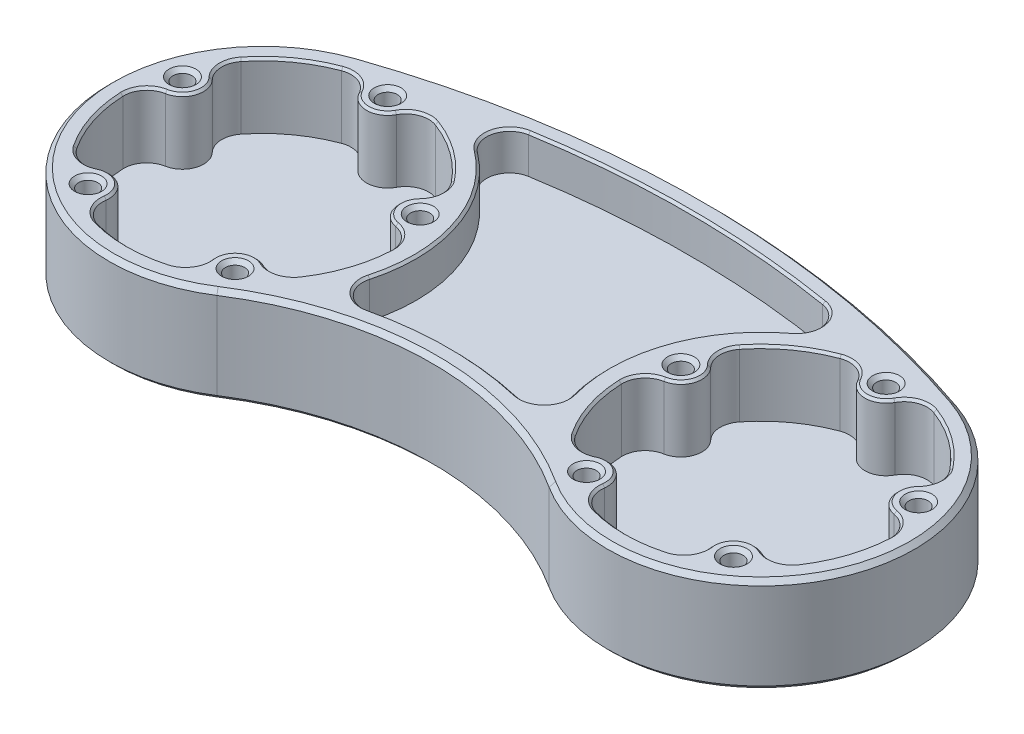
SolidWorks part; units mm, degrees
ref_plane "Front Plane" through (0, 0, 0) normal (0, 0, 1) x (1, 0, 0)
ref_plane "Top Plane" through (0, 0, 0) normal (0, 1, 0) x (1, 0, 0)
ref_plane "Right Plane" through (0, 0, 0) normal (1, 0, 0) x (0, 0, -1)
sketch "Sketch1" plane through (0, 0, 0) normal (0, 1, 0) x (1, 0, 0)
  line L0 (0, 0) -> (0, 64.0532) construction
  line L1 (0, 0) -> (101.1734, 0) construction
  line L2 (-41.275, 25.4) -> (41.275, 25.4) construction
  circle A0 centre (-41.275, 0) radius 25.4
  circle A1 centre (41.275, 0) radius 25.4
  arc A3 (-27.5167, -21.3511) -> (27.5167, -21.3511) centre (0, -64.0532) cw
  arc A4 (-49.53, 24.0211) -> (49.53, 24.0211) centre (0, -120.1057) cw
  dimension "D1" = 82.55
  dimension "D2" = 50.8
  dimension "D3" = 50.8
  dimension "D4" = 152.4
extrude "Boss-Extrude1" add sketch "Sketch1" along normal mid plane 15.875
sketch "Sketch2" plane through (0, 7.9375, 0) normal (0, 1, 0) x (1, 0, 0)
  line L0 (0, 0) -> (0, 31.4381) construction
  circle A0 centre (-41.275, 0) radius 22.225
  arc A1 (-49.53, 24.0211) -> (-27.5167, -21.3511) centre (-41.275, 0) ccw construction
  circle A2 centre (41.275, 0) radius 22.225
  dimension "D1" = 3.175
extrude "Cut-Extrude1" cut sketch "Sketch2" along a picked direction on the side against the normal offset from surface (10.795 mm away) 5.08
sketch "Sketch3" plane through (0, 7.9375, 0) normal (0, 1, 0) x (1, 0, 0)
  arc A0 (24.3588, 27.1178) -> (26.0244, 20.3121) centre (23.7369, 23.3589) cw
  arc A1 (16.7919, -6.7628) -> (12.2544, -11.4877) centre (13.1194, -7.7772) cw
  arc A2 (-12.2544, -11.4877) -> (-16.7919, -6.7628) centre (-13.1194, -7.7772) cw
  arc A3 (-26.0244, 20.3121) -> (-24.3588, 27.1178) centre (-23.7369, 23.3589) cw
  circle A6 centre (-41.275, 0) radius 25.4
  arc A7 (-16.7919, -6.7628) -> (-26.0244, 20.3121) centre (-41.275, 0) ccw
  arc A8 (-48.4981, 21.0185) -> (-29.2365, -18.6822) centre (-41.275, 0) ccw
  arc A9 (29.2365, -18.6822) -> (-29.2365, -18.6822) centre (0, -64.0532) ccw
  arc A10 (29.2365, -18.6822) -> (48.4981, 21.0185) centre (41.275, 0) ccw
  arc A13 (12.2544, -11.4877) -> (-12.2544, -11.4877) centre (0, -64.0532) ccw
  arc A14 (48.4981, 21.0185) -> (-48.4981, 21.0185) centre (0, -120.1057) ccw
  arc A15 (24.3588, 27.1178) -> (-24.3588, 27.1178) centre (0, -120.1057) ccw
  circle A17 centre (41.275, 0) radius 25.4
  arc A18 (26.0244, 20.3121) -> (16.7919, -6.7628) centre (41.275, 0) ccw
  dimension "D4" = 3.81
  dimension "D1" = 3.175
  dimension "D2" = 3.175
  dimension "D3" = 3.175
extrude "Cut-Extrude2" cut sketch "Sketch3" against normal offset from surface (6.35 mm away) 1.5875 up to plane "Top Plane"
mirror "Mirror1" about plane through (0, 0, 0) normal (0, 1, 0) of "Cut-Extrude2"
sketch "Sketch4" plane through (0, -2.8575, 0) normal (0, 1, 0) x (1, 0, 0)
  circle A3 centre (-41.275, 20.701) radius 3.4925
  circle A4 centre (-41.275, 0) radius 20.701
  circle A5 centre (-41.275, 0) radius 20.701 construction
  dimension "D2" = 6.985
  dimension "D1" = 1.524
extrude "Boss-Extrude2" add sketch "Sketch4" along normal up to surface (10.795 mm away)
fillet "Fillet1" radius 3.81 2 edges at (-44.5223, 2.54, -21.9865) (-38.0277, 2.54, -21.9865)
hole_wizard "1/8 (0.125) Diameter Hole1" positions "Sketch6" profile "Sketch5" hole size "1/8" standard "ANSI Inch" end condition through all
sketch "Sketch6" plane through (0, 7.9375, 0) normal (0, 1, 0) x (1, 0, 0)
  arc A0 (-44.3537, 19.0521) -> (-38.1963, 19.0521) centre (-41.275, 20.701) ccw construction
  point P0 (-41.275, 20.701)
sketch "Sketch5" plane through (-41.275, 7.9375, -20.701) normal (1, 0, 0) x (0, 0, 1)
  line L0 (0, 0) -> (0, 15.875)
  line L1 (0, 15.875) -> (2.2225, 15.875)
  line L2 (1.5875, 15.24) -> (1.5875, 0.635)
  line L3 (1.5875, 0.635) -> (2.2225, 0)
  line L5 (2.2225, 0) -> (0, 0)
  line L6 (-1.5875, 0.635) -> (-2.2225, 0) construction
  line L7 (2.2225, 15.875) -> (1.5875, 15.24)
  line L8 (-2.2225, 15.875) -> (-1.5875, 15.24) construction
  line L11 (0, -6.35) -> (0, 107.95) construction
  dimension "Thru Hole Dia." = 3.175
  dimension "Thru Hole Depth" = 15.875
  dimension "Near C'Sink Dia." = 4.445
  dimension "Near C'Sink Angle" = 90
  dimension "Far C'Sink Dia." = 4.445
  dimension "Far C'Sink Angle" = 90
pattern_circular "CirPattern1" count 5 over 360 about axis through (-41.275, 0, 0) along (0, 1, 0) of "1/8 (0.125) Diameter Hole1", "Boss-Extrude2", "Fillet1"
sketch "Sketch7" plane through (0, 7.9375, 0) normal (0, 1, 0) x (1, 0, 0)
  line L1 (0, 25.4) -> (66.675, 25.4)
  line L2 (0, 25.4) -> (0, -25.4)
  line L3 (0, -25.4) -> (66.675, -25.4)
  line L4 (66.675, 25.4) -> (66.675, -25.4)
  arc A0 (27.5167, -21.3511) -> (49.53, 24.0211) centre (41.275, 0) ccw construction
extrude "Cut-Extrude3" cut sketch "Sketch7" against normal through all
mirror "Mirror8" about plane through (0, -7.9375, -25.4) normal (-1, 0, 0) of bodies 108
chamfer "Chamfer1" distance 0.381 angle 45 56 edges at (-57.6413, 7.9375, -5.3177) (-62.4122, 7.9375, 6.8679) (-62.6472, 7.9375, -1.5906) (-59.5004, 7.9375, -11.2755) (-51.3899, 7.9375, 13.922) (-41.275, 7.9375, 22.225) (-49.3921, 7.9375, 19.8346) (-57.6305, 7.9375, 13.849) (-31.1601, 7.9375, 13.922) (-20.1378, 7.9375, 6.8679) (-24.9195, 7.9375, 13.849) (-33.1579, 7.9375, 19.8346) (-24.9087, 7.9375, -5.3177) (-28.2115, 7.9375, -17.9804) (-23.0496, 7.9375, -11.2755) (-19.9028, 7.9375, -1.5906) (27.4376, -7.9375, -24.2646) (27.4376, 7.9375, -24.2646) (0, 7.9375, -29.1193) (-27.4376, 7.9375, -24.2646) (28.2115, 7.9375, -17.9804) (-17.2343, 7.9375, -8.1979) (54.3385, 7.9375, -17.9804) (62.4122, 7.9375, 6.8679) (41.275, 7.9375, 22.225) (20.1378, 7.9375, 6.8679) (17.2343, 7.9375, -8.1979) (15.8674, 7.9375, 10.4162) (-15.8674, 7.9375, 10.4162) (17.2343, -7.9375, -8.1979) (0, 7.9375, 10.0782) (15.8674, -7.9375, 10.4162) (41.275, 7.9375, -17.2085) (46.3667, 7.9375, -20.8176) (36.1833, 7.9375, -20.8176) (57.6413, 7.9375, -5.3177) (51.3899, 7.9375, 13.922) (31.1601, 7.9375, 13.922) (24.9087, 7.9375, -5.3177) (62.6472, 7.9375, -1.5906) (59.5004, 7.9375, -11.2755) (49.3921, 7.9375, 19.8346) (57.6305, 7.9375, 13.849) (24.9195, 7.9375, 13.849) (33.1579, 7.9375, 19.8346) (23.0496, 7.9375, -11.2755) (19.9028, 7.9375, -1.5906) (0, -7.9375, -29.1193) (-27.4376, -7.9375, -24.2646) (-17.2343, -7.9375, -8.1979) (-15.8674, -7.9375, 10.4162) (0, -7.9375, 10.0782) (-41.275, 7.9375, -17.2085) (-54.3385, 7.9375, -17.9804) (-46.3667, 7.9375, -20.8176) (-36.1833, 7.9375, -20.8176)
chamfer "Chamfer2" distance 0.762 angle 45 8 edges at (0, 7.9375, -32.2943) (64.1274, -7.9375, 11.0873) (64.1274, 7.9375, 11.0873) (-64.1274, 7.9375, 11.0873) (0, -7.9375, -32.2943) (0, -7.9375, 13.2532) (-64.1274, -7.9375, 11.0873) (0, 7.9375, 13.2532)
